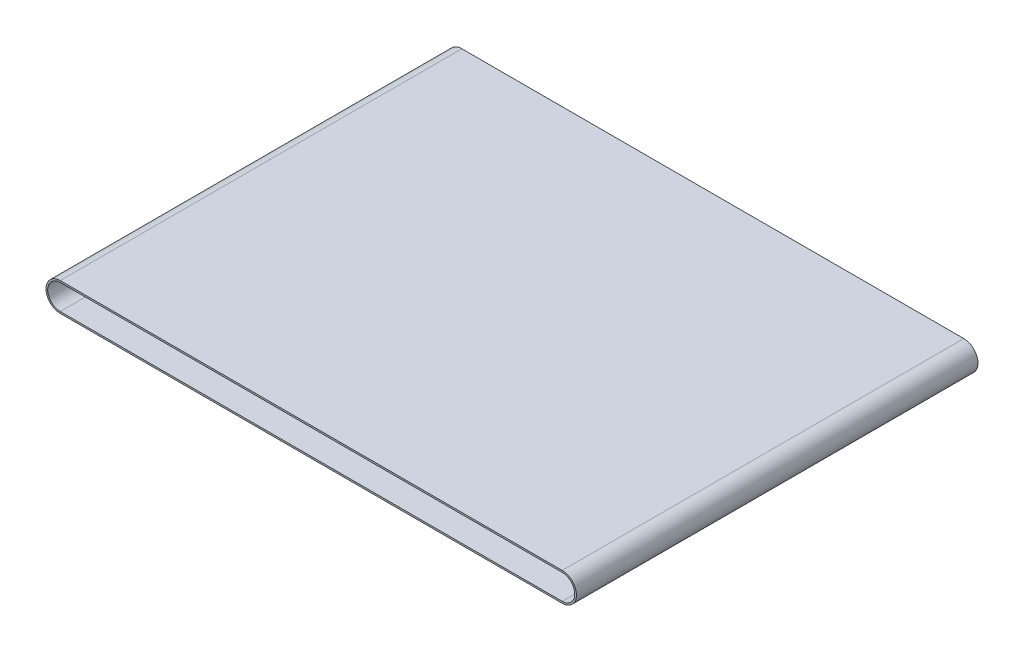
SolidWorks part; units mm, degrees
ref_plane "Front Plane" through (0, 0, 0) normal (0, 0, 1) x (1, 0, 0)
ref_plane "Top Plane" through (0, 0, 0) normal (0, 1, 0) x (1, 0, 0)
ref_plane "Right Plane" through (0, 0, 0) normal (1, 0, 0) x (0, 0, -1)
sketch "Sketch1" plane through (0, 0, 0) normal (0, 0, 1) x (1, 0, 0)
  line L0 (-60.6868, 26.7882) -> (239.3132, 26.7882)
  line L1 (-60.6868, 9.7882) -> (239.3132, 9.7882)
  line L2 (-60.6868, 10.7882) -> (239.3132, 10.7882)
  line L3 (-60.6868, 25.7882) -> (239.3132, 25.7882)
  arc A0 (-60.6868, 26.7882) -> (-60.6868, 9.7882) centre (-60.6868, 18.2882) ccw
  arc A1 (239.3132, 26.7882) -> (239.3132, 9.7882) centre (239.3132, 18.2882) cw
  arc A2 (239.3132, 25.7882) -> (239.3132, 10.7882) centre (239.3132, 18.2882) cw
  arc A3 (-60.6868, 25.7882) -> (-60.6868, 10.7882) centre (-60.6868, 18.2882) ccw
  dimension "D3" = 8.5
  dimension "D2" = 300
  dimension "D1" = 1
extrude "Boss-Extrude1" add sketch "Sketch1" along normal blind 240
